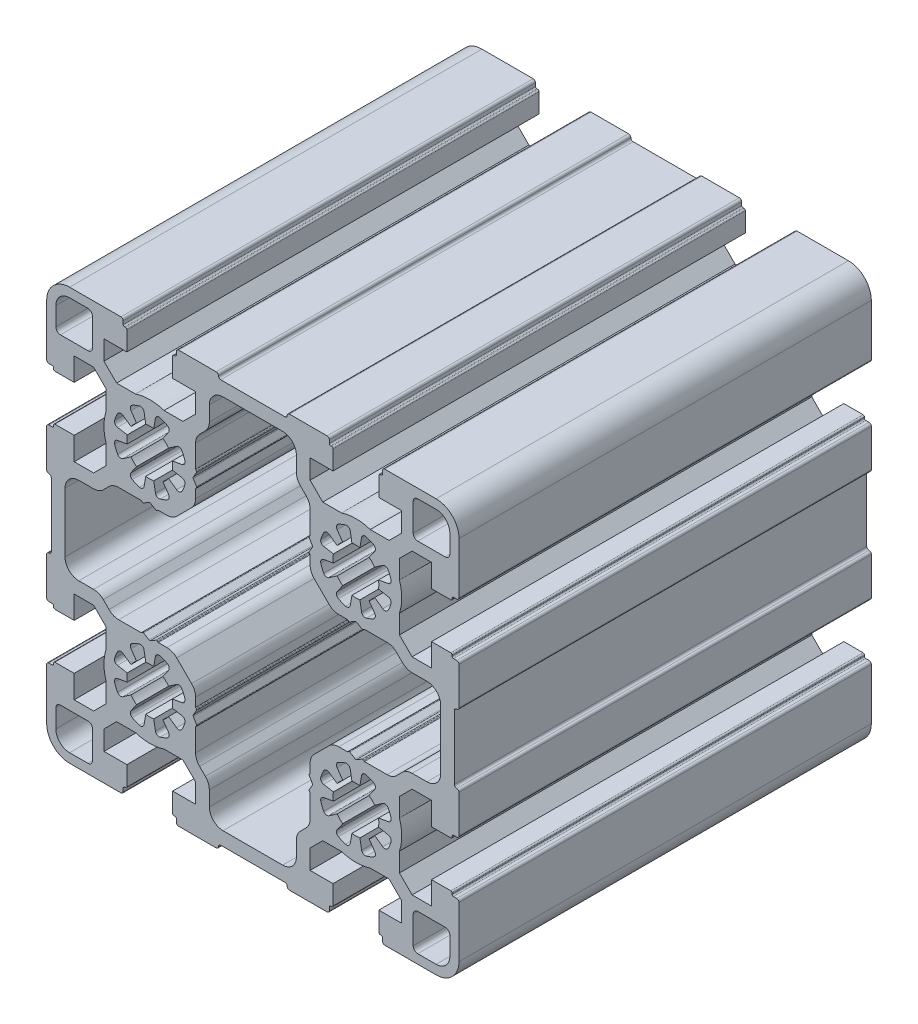
SolidWorks part; units mm, degrees
ref_plane "Front Plane" through (0, 0, 0) normal (0, 0, 1) x (1, 0, 0)
ref_plane "Top Plane" through (0, 0, 0) normal (0, 1, 0) x (1, 0, 0)
ref_plane "Right Plane" through (0, 0, 0) normal (1, 0, 0) x (0, 0, -1)
sketch "Sketch1" plane through (0, 0, 0) normal (0, 0, 1) x (1, 0, 0)
  line L0 (12.5001, -34.7627) -> (15.2628, -32)
  line L1 (15.2628, -32) -> (19.3776, -32)
  line L2 (25.6225, -32) -> (29.7373, -32)
  line L3 (29.7373, -32) -> (32.5, -34.7627)
  line L4 (32.5, -34.7627) -> (32.5, -39)
  line L5 (32.5, -39) -> (27.5002, -39)
  line L6 (27.5002, -39) -> (27.5002, -43.2)
  line L7 (27.8002, -43.5) -> (28.0002, -43.5)
  line L8 (28.3002, -44.5) -> (28.3002, -43.8)
  line L9 (28.8002, -45) -> (40, -45)
  line L10 (45, -40) -> (45, -28.7999)
  line L11 (43.8, -28.2999) -> (44.5, -28.2999)
  line L12 (43.5, -27.9999) -> (43.5, -27.7999)
  line L13 (43.2, -27.4999) -> (39.0002, -27.4999)
  line L14 (39.0002, -27.4999) -> (39.0002, -32.4999)
  line L15 (39.0002, -32.4999) -> (34.7629, -32.4999)
  line L16 (34.7629, -32.4999) -> (32.0002, -29.7372)
  line L17 (32.0002, -29.7372) -> (32.0002, -25.6224)
  line L18 (32.0002, -19.3775) -> (32.0002, -15.2627)
  line L19 (32.0002, -15.2627) -> (34.7629, -12.5)
  line L20 (34.7629, -12.5) -> (39, -12.5)
  line L21 (39, -12.5) -> (39, -17.5)
  line L22 (39, -17.5) -> (43.2, -17.5)
  line L23 (43.5, -17.2) -> (43.5, -17)
  line L24 (43.8, -16.7) -> (44.5, -16.7)
  line L25 (45, -16.2) -> (45, -8)
  line L26 (44, -7) -> (44, 7)
  line L27 (45, 8) -> (45, 16.2)
  line L28 (43.8, 16.7) -> (44.5, 16.7)
  line L29 (43.5, 17) -> (43.5, 17.2)
  line L30 (43.2, 17.5) -> (39.0002, 17.5)
  line L31 (39.0002, 17.5) -> (39.0002, 12.5)
  line L32 (39.0002, 12.5) -> (34.7629, 12.5)
  line L33 (34.7629, 12.5) -> (32.0002, 15.2628)
  line L34 (32.0002, 15.2628) -> (32.0002, 19.3775)
  line L35 (32.0002, 25.6225) -> (32.0002, 29.7372)
  line L36 (32.0002, 29.7372) -> (34.7629, 32.5)
  line L37 (34.7629, 32.5) -> (39, 32.5)
  line L38 (39, 32.5) -> (39, 27.5001)
  line L39 (39, 27.5001) -> (43.2, 27.5001)
  line L40 (43.5, 27.8001) -> (43.5, 28.0001)
  line L41 (43.8, 28.3001) -> (44.5, 28.3001)
  line L42 (45, 28.8001) -> (45, 40)
  line L43 (28.8, 45) -> (40, 45)
  line L44 (28.3, 43.8) -> (28.3, 44.5)
  line L45 (27.8, 43.5) -> (28, 43.5)
  line L46 (27.5, 43.2) -> (27.5, 39)
  line L47 (27.5, 39) -> (32.4999, 39)
  line L48 (32.4999, 39) -> (32.4999, 34.7628)
  line L49 (32.4999, 34.7628) -> (29.7371, 32)
  line L50 (29.7371, 32) -> (25.6224, 32)
  line L51 (19.3774, 32) -> (15.2626, 32)
  line L52 (15.2626, 32) -> (12.4999, 34.7628)
  line L53 (12.4999, 34.7628) -> (12.4999, 39)
  line L54 (12.4999, 39) -> (17.4999, 39)
  line L55 (17.4999, 39) -> (17.4999, 43.2)
  line L56 (16.9999, 43.5) -> (17.1999, 43.5)
  line L57 (16.6999, 43.8) -> (16.6999, 44.5)
  line L58 (7.9999, 45) -> (16.1999, 45)
  line L59 (-7.0001, 44) -> (6.9999, 44)
  line L60 (-16.2, 45) -> (-8.0001, 45)
  line L61 (-16.7, 43.8) -> (-16.7, 44.5)
  line L62 (-17.2, 43.5) -> (-17, 43.5)
  line L63 (-17.5, 43.2) -> (-17.5, 39)
  line L64 (-17.5, 39) -> (-12.5001, 39)
  line L65 (-12.5001, 39) -> (-12.5001, 34.7628)
  line L66 (-12.5001, 34.7628) -> (-15.2628, 32)
  line L67 (-15.2628, 32) -> (-19.3776, 32)
  line L68 (-25.6225, 32) -> (-29.7373, 32)
  line L69 (-29.7373, 32) -> (-32.5, 34.7628)
  line L70 (-32.5, 34.7628) -> (-32.5, 39)
  line L71 (-32.5, 39) -> (-27.5, 39)
  line L72 (-27.5, 39) -> (-27.5, 43.2)
  line L73 (-28, 43.5) -> (-27.8, 43.5)
  line L74 (-28.3, 43.8) -> (-28.3, 44.5)
  line L75 (-40, 45) -> (-28.8, 45)
  line L76 (-45, 28.7999) -> (-45, 40)
  line L77 (-44.5, 28.2999) -> (-43.8, 28.2999)
  line L78 (-43.5, 27.7999) -> (-43.5, 27.9999)
  line L79 (-43.2, 27.4999) -> (-39, 27.4999)
  line L80 (-39, 27.4999) -> (-39, 32.4999)
  line L81 (-39, 32.4999) -> (-34.7628, 32.4999)
  line L82 (-34.7628, 32.4999) -> (-32, 29.7372)
  line L83 (-32, 29.7372) -> (-32, 25.6224)
  line L84 (-32, 19.3775) -> (-32, 15.2627)
  line L85 (-32, 15.2627) -> (-34.7628, 12.5)
  line L86 (-34.7628, 12.5) -> (-39, 12.5)
  line L87 (-39, 12.5) -> (-39, 17.5)
  line L88 (-39, 17.5) -> (-43.2, 17.5)
  line L89 (-43.5, 17) -> (-43.5, 17.2)
  line L90 (-44.5, 16.7) -> (-43.8, 16.7)
  line L91 (-45, 8) -> (-45, 16.2)
  line L92 (-44, -7) -> (-44, 7)
  line L93 (-45, -16.2) -> (-45, -8)
  line L94 (-44.5, -16.7) -> (-43.8, -16.7)
  line L95 (-43.5, -17.2) -> (-43.5, -17)
  line L96 (-43.2, -17.5) -> (-39, -17.5)
  line L97 (-39, -17.5) -> (-39, -12.5)
  line L98 (-39, -12.5) -> (-34.7628, -12.5)
  line L99 (-34.7628, -12.5) -> (-32, -15.2627)
  line L100 (-32, -15.2627) -> (-32, -19.3775)
  line L101 (-32, -25.6224) -> (-32, -29.7372)
  line L102 (-32, -29.7372) -> (-34.7628, -32.4999)
  line L103 (-34.7628, -32.4999) -> (-39, -32.4999)
  line L104 (-39, -32.4999) -> (-39, -27.4999)
  line L105 (-39, -27.4999) -> (-43.2, -27.4999)
  line L106 (-43.5, -27.9999) -> (-43.5, -27.7999)
  line L107 (-44.5, -28.2999) -> (-43.8, -28.2999)
  line L108 (-45, -40) -> (-45, -28.7999)
  line L109 (-40, -45) -> (-28.8, -45)
  line L110 (-28.3, -44.5) -> (-28.3, -43.8)
  line L111 (-28, -43.5) -> (-27.8, -43.5)
  line L112 (-27.5, -43.2) -> (-27.5, -39)
  line L113 (-27.5, -39) -> (-32.5, -39)
  line L114 (-32.5, -39) -> (-32.5, -34.7628)
  line L115 (-32.5, -34.7628) -> (-29.7373, -32)
  line L116 (-29.7373, -32) -> (-25.6225, -32)
  line L117 (-19.3776, -32) -> (-15.2628, -32)
  line L118 (-15.2628, -32) -> (-12.5001, -34.7628)
  line L119 (-12.5001, -34.7628) -> (-12.5001, -39)
  line L120 (-12.5001, -39) -> (-17.5001, -39)
  line L121 (-17.5001, -39) -> (-17.5001, -43.2)
  line L122 (-17.2001, -43.5) -> (-17.0001, -43.5)
  line L123 (-16.7001, -44.5) -> (-16.7001, -43.8)
  line L124 (-16.2001, -45) -> (-8.0001, -45)
  line L125 (-7.0001, -44) -> (6.9999, -44)
  line L126 (7.9999, -45) -> (16.1999, -45)
  line L127 (16.6999, -44.5) -> (16.6999, -43.8)
  line L128 (16.9999, -43.5) -> (17.1999, -43.5)
  line L129 (17.4999, -43.2) -> (17.4999, -39)
  line L130 (17.4999, -39) -> (12.5001, -39)
  line L131 (12.5001, -39) -> (12.5001, -34.7627)
  line L132 (12.2948, -21.1329) -> (12.989, -22.3353)
  line L133 (12.2779, -23.867) -> (12.989, -22.6353)
  line L134 (12.3097, -24.1085) -> (12.4414, -24.2402)
  line L135 (12.5, -29.2774) -> (12.5, -24.3816)
  line L136 (10.3787, -32.6414) -> (11.6213, -31.3987)
  line L137 (9.5, -37.9999) -> (9.5, -34.7627)
  line L138 (-6.5, -40.9999) -> (6.5, -40.9999)
  line L139 (-9.5, -37.9999) -> (-9.5, -34.7627)
  line L140 (-10.3787, -32.6414) -> (-11.6213, -31.3987)
  line L141 (-12.5, -29.2774) -> (-12.5, -24.3816)
  line L142 (-12.4414, -24.2402) -> (-12.3097, -24.1085)
  line L143 (-12.2779, -23.867) -> (-12.989, -22.6353)
  line L144 (-12.989, -22.3353) -> (-12.2948, -21.1329)
  line L145 (-12.3266, -20.8914) -> (-12.4414, -20.7766)
  line L146 (-12.5, -20.6352) -> (-12.5, -18.7426)
  line L147 (-13.3787, -16.6213) -> (-16.6213, -13.3787)
  line L148 (-20.6352, -12.5) -> (-18.7426, -12.5)
  line L149 (-20.7766, -12.4414) -> (-20.8914, -12.3266)
  line L150 (-22.3353, -12.989) -> (-21.1329, -12.2948)
  line L151 (-22.6353, -12.989) -> (-23.867, -12.2779)
  line L152 (-24.2402, -12.4414) -> (-24.1085, -12.3097)
  line L153 (-29.2774, -12.5) -> (-24.3816, -12.5)
  line L154 (-31.3987, -11.6213) -> (-32.6414, -10.3787)
  line L155 (-37.9999, -9.5) -> (-34.7627, -9.5)
  line L156 (-40.9999, -6.5) -> (-40.9999, 6.5)
  line L157 (-37.9999, 9.5) -> (-34.7627, 9.5)
  line L158 (-32.6414, 10.3787) -> (-31.3987, 11.6213)
  line L159 (-29.2774, 12.5) -> (-24.3816, 12.5)
  line L160 (-24.2402, 12.4414) -> (-24.1085, 12.3097)
  line L161 (-23.867, 12.2779) -> (-22.6353, 12.989)
  line L162 (-22.3353, 12.989) -> (-21.1329, 12.2948)
  line L163 (-20.8914, 12.3266) -> (-20.7766, 12.4414)
  line L164 (-20.6352, 12.5) -> (-18.7426, 12.5)
  line L165 (-16.6213, 13.3787) -> (-13.3787, 16.6213)
  line L166 (-12.5, 18.7426) -> (-12.5, 20.6352)
  line L167 (-12.4414, 20.7766) -> (-12.3266, 20.8914)
  line L168 (-12.2948, 21.1329) -> (-12.989, 22.3353)
  line L169 (-12.989, 22.6353) -> (-12.2779, 23.867)
  line L170 (-12.3097, 24.1085) -> (-12.4414, 24.2402)
  line L171 (-12.5, 24.3816) -> (-12.5, 29.2774)
  line L172 (-11.6213, 31.3987) -> (-10.3787, 32.6414)
  line L173 (-9.5, 34.7627) -> (-9.5, 37.9999)
  line L174 (-6.5, 40.9999) -> (6.5, 40.9999)
  line L175 (9.5, 34.7627) -> (9.5, 37.9999)
  line L176 (10.3787, 32.6414) -> (11.6213, 31.3987)
  line L177 (12.5, 24.3816) -> (12.5, 29.2774)
  line L178 (12.3097, 24.1085) -> (12.4414, 24.2402)
  line L179 (12.2779, 23.867) -> (12.989, 22.6353)
  line L180 (12.2948, 21.1329) -> (12.989, 22.3353)
  line L181 (12.3266, 20.8914) -> (12.4414, 20.7766)
  line L182 (12.5, 18.7426) -> (12.5, 20.6352)
  line L183 (13.3787, 16.6213) -> (16.6213, 13.3787)
  line L184 (18.7426, 12.5) -> (20.6352, 12.5)
  line L185 (20.7766, 12.4414) -> (20.8914, 12.3266)
  line L186 (21.1329, 12.2948) -> (22.3353, 12.989)
  line L187 (22.6353, 12.989) -> (23.867, 12.2779)
  line L188 (24.1085, 12.3097) -> (24.2402, 12.4414)
  line L189 (24.3816, 12.5) -> (29.2774, 12.5)
  line L190 (31.3987, 11.6213) -> (32.6414, 10.3787)
  line L191 (34.7627, 9.5) -> (37.9999, 9.5)
  line L192 (40.9999, -6.5) -> (40.9999, 6.5)
  line L193 (34.7627, -9.5) -> (37.9999, -9.5)
  line L194 (31.3987, -11.6213) -> (32.6414, -10.3787)
  line L195 (24.3816, -12.5) -> (29.2774, -12.5)
  line L196 (24.2402, -12.4414) -> (24.1085, -12.3097)
  line L197 (22.6353, -12.989) -> (23.867, -12.2779)
  line L198 (22.3353, -12.989) -> (21.1329, -12.2948)
  line L199 (20.7766, -12.4414) -> (20.8914, -12.3266)
  line L200 (18.7426, -12.5) -> (20.6352, -12.5)
  line L201 (13.3787, -16.6213) -> (16.6213, -13.3787)
  line L202 (12.5, -20.6352) -> (12.5, -18.7426)
  line L203 (12.3266, -20.8914) -> (12.4414, -20.7766)
  line L204 (-18.3958, -28.3613) -> (-19.6321, -26.5957)
  line L205 (-18.4042, -25.3679) -> (-16.6386, -26.6041)
  line L206 (-15.4533, -23.7425) -> (-17.576, -23.3682)
  line L207 (-17.576, -21.6317) -> (-15.4533, -21.2575)
  line L208 (-18.4042, -19.6321) -> (-16.6386, -18.3958)
  line L209 (-19.6321, -18.4043) -> (-18.3958, -16.6387)
  line L210 (-21.6317, -17.576) -> (-21.2574, -15.4533)
  line L211 (-23.3682, -17.576) -> (-23.7425, -15.4533)
  line L212 (-26.6041, -16.6386) -> (-25.3678, -18.4043)
  line L213 (-26.5957, -19.6321) -> (-28.3613, -18.3958)
  line L214 (-29.5466, -21.2575) -> (-27.424, -21.6318)
  line L215 (-29.5466, -23.7425) -> (-27.424, -23.3682)
  line L216 (-28.3613, -26.6042) -> (-26.5957, -25.3679)
  line L217 (-26.6041, -28.3613) -> (-25.3678, -26.5957)
  line L218 (-23.7425, -29.5467) -> (-23.3682, -27.424)
  line L219 (-21.6317, -27.424) -> (-21.2574, -29.5467)
  line L220 (26.6041, -28.3613) -> (25.3678, -26.5957)
  line L221 (26.5957, -25.3678) -> (28.3613, -26.6041)
  line L222 (29.5466, -23.7425) -> (27.4239, -23.3682)
  line L223 (27.4239, -21.6317) -> (29.5466, -21.2575)
  line L224 (26.5957, -19.6321) -> (28.3613, -18.3958)
  line L225 (25.3678, -18.4042) -> (26.6041, -16.6386)
  line L226 (23.3682, -17.576) -> (23.7425, -15.4533)
  line L227 (21.6317, -17.5759) -> (21.2574, -15.4533)
  line L228 (18.3958, -16.6386) -> (19.6321, -18.4042)
  line L229 (18.4042, -19.6321) -> (16.6386, -18.3958)
  line L230 (15.4533, -21.2574) -> (17.5759, -21.6317)
  line L231 (15.4533, -23.7425) -> (17.5759, -23.3682)
  line L232 (16.6386, -26.6041) -> (18.4042, -25.3678)
  line L233 (18.3958, -28.3613) -> (19.6321, -26.5957)
  line L234 (21.2574, -29.5466) -> (21.6317, -27.424)
  line L235 (23.3682, -27.424) -> (23.7425, -29.5466)
  line L236 (-34.9999, -41.9999) -> (-34.9999, -35.9999)
  line L237 (-39.9999, -42.9999) -> (-35.9999, -42.9999)
  line L238 (-42.9999, -39.9999) -> (-42.9999, -35.9999)
  line L239 (-41.9999, -34.9999) -> (-35.9999, -34.9999)
  line L240 (34.9999, -41.9999) -> (34.9999, -35.9999)
  line L241 (35.9999, -42.9999) -> (39.9999, -42.9999)
  line L242 (42.9999, -39.9999) -> (42.9999, -35.9999)
  line L243 (35.9999, -34.9999) -> (41.9999, -34.9999)
  line L244 (-18.3958, 16.6386) -> (-19.6321, 18.4042)
  line L245 (-18.4042, 19.6321) -> (-16.6386, 18.3958)
  line L246 (-15.4532, 21.2574) -> (-17.5759, 21.6317)
  line L247 (-17.5759, 23.3682) -> (-15.4532, 23.7425)
  line L248 (-18.4042, 25.3679) -> (-16.6386, 26.6042)
  line L249 (-19.6321, 26.5957) -> (-18.3958, 28.3613)
  line L250 (-21.6317, 27.424) -> (-21.2574, 29.5467)
  line L251 (-23.3682, 27.424) -> (-23.7425, 29.5467)
  line L252 (-26.6041, 28.3613) -> (-25.3678, 26.5957)
  line L253 (-26.5957, 25.3678) -> (-28.3613, 26.6041)
  line L254 (-29.5467, 23.7425) -> (-27.424, 23.3682)
  line L255 (-29.5467, 21.2574) -> (-27.424, 21.6317)
  line L256 (-28.3613, 18.3958) -> (-26.5957, 19.6321)
  line L257 (-26.6041, 16.6386) -> (-25.3678, 18.4042)
  line L258 (-23.7425, 15.4533) -> (-23.3682, 17.5759)
  line L259 (-21.6317, 17.5759) -> (-21.2574, 15.4533)
  line L260 (26.6041, 16.6386) -> (25.3678, 18.4042)
  line L261 (26.5957, 19.6321) -> (28.3613, 18.3958)
  line L262 (29.5466, 21.2575) -> (27.4239, 21.6317)
  line L263 (27.4239, 23.3682) -> (29.5466, 23.7424)
  line L264 (26.5957, 25.3678) -> (28.3613, 26.6041)
  line L265 (25.3678, 26.5957) -> (26.6041, 28.3613)
  line L266 (23.3682, 27.424) -> (23.7425, 29.5466)
  line L267 (21.6317, 27.424) -> (21.2574, 29.5466)
  line L268 (18.3958, 28.3613) -> (19.6321, 26.5957)
  line L269 (18.4042, 25.3678) -> (16.6386, 26.6041)
  line L270 (15.4533, 23.7425) -> (17.5759, 23.3682)
  line L271 (15.4533, 21.2574) -> (17.5759, 21.6317)
  line L272 (16.6386, 18.3958) -> (18.4042, 19.6321)
  line L273 (18.3958, 16.6386) -> (19.6321, 18.4042)
  line L274 (21.2574, 15.4533) -> (21.6317, 17.5759)
  line L275 (23.3682, 17.576) -> (23.7425, 15.4533)
  line L276 (-34.9999, 35.9999) -> (-34.9999, 41.9999)
  line L277 (-39.9999, 42.9999) -> (-35.9999, 42.9999)
  line L278 (-42.9999, 35.9999) -> (-42.9999, 39.9999)
  line L279 (-41.9999, 34.9999) -> (-35.9999, 34.9999)
  line L280 (34.9999, 35.9999) -> (34.9999, 41.9999)
  line L281 (35.9999, 42.9999) -> (39.9999, 42.9999)
  line L282 (42.9999, 35.9999) -> (42.9999, 39.9999)
  line L283 (35.9999, 34.9999) -> (41.9999, 34.9999)
  line L284 (0, 52.3629) -> (0, -57.313) construction
  line L285 (-58.4117, 0) -> (63.1855, 0) construction
  arc A0 (19.3776, -32) -> (25.6225, -32) centre (22.5, -22.5) ccw
  arc A1 (27.5002, -43.2) -> (27.8002, -43.5) centre (27.8002, -43.2) ccw
  arc A2 (28.3002, -43.8) -> (28.0002, -43.5) centre (28.0002, -43.8) ccw
  arc A3 (28.3002, -44.5) -> (28.8002, -45) centre (28.8002, -44.5) ccw
  arc A4 (40, -45) -> (45, -40) centre (40, -40) ccw
  arc A5 (45, -28.7999) -> (44.5, -28.2999) centre (44.5, -28.7999) ccw
  arc A6 (43.5, -27.9999) -> (43.8, -28.2999) centre (43.8, -27.9999) ccw
  arc A7 (43.5, -27.7999) -> (43.2, -27.4999) centre (43.2, -27.7999) ccw
  arc A8 (32.0002, -25.6224) -> (32.0002, -19.3775) centre (22.5002, -22.5) ccw
  arc A9 (43.2, -17.5) -> (43.5, -17.2) centre (43.2, -17.2) ccw
  arc A10 (43.8, -16.7) -> (43.5, -17) centre (43.8, -17) ccw
  arc A11 (44.5, -16.7) -> (45, -16.2) centre (44.5, -16.2) ccw
  arc A12 (45, -8) -> (44.5, -7.5) centre (44.5, -8) ccw
  arc A13 (44, -7) -> (44.5, -7.5) centre (44.5, -7) ccw
  arc A14 (44.5, 7.5) -> (44, 7) centre (44.5, 7) ccw
  arc A15 (44.5, 7.5) -> (45, 8) centre (44.5, 8) ccw
  arc A16 (45, 16.2) -> (44.5, 16.7) centre (44.5, 16.2) ccw
  arc A17 (43.5, 17) -> (43.8, 16.7) centre (43.8, 17) ccw
  arc A18 (43.5, 17.2) -> (43.2, 17.5) centre (43.2, 17.2) ccw
  arc A19 (32.0002, 19.3775) -> (32.0002, 25.6225) centre (22.5002, 22.5) ccw
  arc A20 (43.2, 27.5001) -> (43.5, 27.8001) centre (43.2, 27.8001) ccw
  arc A21 (43.8, 28.3001) -> (43.5, 28.0001) centre (43.8, 28.0001) ccw
  arc A22 (44.5, 28.3001) -> (45, 28.8001) centre (44.5, 28.8001) ccw
  arc A23 (45, 40) -> (40, 45) centre (40, 40) ccw
  arc A24 (28.8, 45) -> (28.3, 44.5) centre (28.8, 44.5) ccw
  arc A25 (28, 43.5) -> (28.3, 43.8) centre (28, 43.8) ccw
  arc A26 (27.8, 43.5) -> (27.5, 43.2) centre (27.8, 43.2) ccw
  arc A27 (25.6224, 32) -> (19.3774, 32) centre (22.4999, 22.5) ccw
  arc A28 (17.4999, 43.2) -> (17.1999, 43.5) centre (17.1999, 43.2) ccw
  arc A29 (16.6999, 43.8) -> (16.9999, 43.5) centre (16.9999, 43.8) ccw
  arc A30 (16.6999, 44.5) -> (16.1999, 45) centre (16.1999, 44.5) ccw
  arc A31 (7.9999, 45) -> (7.4999, 44.5) centre (7.9999, 44.5) ccw
  arc A32 (6.9999, 44) -> (7.4999, 44.5) centre (6.9999, 44.5) ccw
  arc A33 (-7.5001, 44.5) -> (-7.0001, 44) centre (-7.0001, 44.5) ccw
  arc A34 (-7.5001, 44.5) -> (-8.0001, 45) centre (-8.0001, 44.5) ccw
  arc A35 (-16.2, 45) -> (-16.7, 44.5) centre (-16.2, 44.5) ccw
  arc A36 (-17, 43.5) -> (-16.7, 43.8) centre (-17, 43.8) ccw
  arc A37 (-17.2, 43.5) -> (-17.5, 43.2) centre (-17.2, 43.2) ccw
  arc A38 (-19.3776, 32) -> (-25.6225, 32) centre (-22.5, 22.5) ccw
  arc A39 (-27.5, 43.2) -> (-27.8, 43.5) centre (-27.8, 43.2) ccw
  arc A40 (-28.3, 43.8) -> (-28, 43.5) centre (-28, 43.8) ccw
  arc A41 (-28.3, 44.5) -> (-28.8, 45) centre (-28.8, 44.5) ccw
  arc A42 (-40, 45) -> (-45, 40) centre (-40, 40) ccw
  arc A43 (-45, 28.7999) -> (-44.5, 28.2999) centre (-44.5, 28.7999) ccw
  arc A44 (-43.5, 27.9999) -> (-43.8, 28.2999) centre (-43.8, 27.9999) ccw
  arc A45 (-43.5, 27.7999) -> (-43.2, 27.4999) centre (-43.2, 27.7999) ccw
  arc A46 (-32, 25.6224) -> (-32, 19.3775) centre (-22.5, 22.5) ccw
  arc A47 (-43.2, 17.5) -> (-43.5, 17.2) centre (-43.2, 17.2) ccw
  arc A48 (-43.8, 16.7) -> (-43.5, 17) centre (-43.8, 17) ccw
  arc A49 (-44.5, 16.7) -> (-45, 16.2) centre (-44.5, 16.2) ccw
  arc A50 (-45, 8) -> (-44.5, 7.5) centre (-44.5, 8) ccw
  arc A51 (-44, 7) -> (-44.5, 7.5) centre (-44.5, 7) ccw
  arc A52 (-44.5, -7.5) -> (-44, -7) centre (-44.5, -7) ccw
  arc A53 (-44.5, -7.5) -> (-45, -8) centre (-44.5, -8) ccw
  arc A54 (-45, -16.2) -> (-44.5, -16.7) centre (-44.5, -16.2) ccw
  arc A55 (-43.5, -17) -> (-43.8, -16.7) centre (-43.8, -17) ccw
  arc A56 (-43.5, -17.2) -> (-43.2, -17.5) centre (-43.2, -17.2) ccw
  arc A57 (-32, -19.3775) -> (-32, -25.6224) centre (-22.5, -22.5) ccw
  arc A58 (-43.2, -27.4999) -> (-43.5, -27.7999) centre (-43.2, -27.7999) ccw
  arc A59 (-43.8, -28.2999) -> (-43.5, -27.9999) centre (-43.8, -27.9999) ccw
  arc A60 (-44.5, -28.2999) -> (-45, -28.7999) centre (-44.5, -28.7999) ccw
  arc A61 (-45, -40) -> (-40, -45) centre (-40, -40) ccw
  arc A62 (-28.8, -45) -> (-28.3, -44.5) centre (-28.8, -44.5) ccw
  arc A63 (-28, -43.5) -> (-28.3, -43.8) centre (-28, -43.8) ccw
  arc A64 (-27.8, -43.5) -> (-27.5, -43.2) centre (-27.8, -43.2) ccw
  arc A65 (-25.6225, -32) -> (-19.3776, -32) centre (-22.5, -22.5) ccw
  arc A66 (-17.5001, -43.2) -> (-17.2001, -43.5) centre (-17.2001, -43.2) ccw
  arc A67 (-16.7001, -43.8) -> (-17.0001, -43.5) centre (-17.0001, -43.8) ccw
  arc A68 (-16.7001, -44.5) -> (-16.2001, -45) centre (-16.2001, -44.5) ccw
  arc A69 (-8.0001, -45) -> (-7.5001, -44.5) centre (-8.0001, -44.5) ccw
  arc A70 (-7.0001, -44) -> (-7.5001, -44.5) centre (-7.0001, -44.5) ccw
  arc A71 (7.4999, -44.5) -> (6.9999, -44) centre (6.9999, -44.5) ccw
  arc A72 (7.4999, -44.5) -> (7.9999, -45) centre (7.9999, -44.5) ccw
  arc A73 (16.1999, -45) -> (16.6999, -44.5) centre (16.1999, -44.5) ccw
  arc A74 (16.9999, -43.5) -> (16.6999, -43.8) centre (16.9999, -43.8) ccw
  arc A75 (17.1999, -43.5) -> (17.4999, -43.2) centre (17.1999, -43.2) ccw
  arc A76 (12.3266, -20.8914) -> (12.2948, -21.1329) centre (12.468, -21.0329) ccw
  arc A77 (12.989, -22.6353) -> (12.989, -22.3353) centre (12.7292, -22.4853) ccw
  arc A78 (12.2779, -23.867) -> (12.3097, -24.1085) centre (12.4511, -23.967) ccw
  arc A79 (12.5, -24.3816) -> (12.4414, -24.2402) centre (12.3, -24.3816) ccw
  arc A80 (11.6213, -31.3987) -> (12.5, -29.2774) centre (9.5, -29.2774) ccw
  arc A81 (10.3787, -32.6414) -> (9.5, -34.7627) centre (12.5, -34.7627) ccw
  arc A82 (6.5, -40.9999) -> (9.5, -37.9999) centre (6.5, -37.9999) ccw
  arc A83 (-9.5, -37.9999) -> (-6.5, -40.9999) centre (-6.5, -37.9999) ccw
  arc A84 (-9.5, -34.7627) -> (-10.3787, -32.6414) centre (-12.5, -34.7627) ccw
  arc A85 (-12.5, -29.2774) -> (-11.6213, -31.3987) centre (-9.5, -29.2774) ccw
  arc A86 (-12.4414, -24.2402) -> (-12.5, -24.3816) centre (-12.3, -24.3816) ccw
  arc A87 (-12.3097, -24.1085) -> (-12.2779, -23.867) centre (-12.4511, -23.967) ccw
  arc A88 (-12.989, -22.3353) -> (-12.989, -22.6353) centre (-12.7292, -22.4853) ccw
  arc A89 (-12.2948, -21.1329) -> (-12.3266, -20.8914) centre (-12.468, -21.0329) ccw
  arc A90 (-12.5, -20.6352) -> (-12.4414, -20.7766) centre (-12.3, -20.6352) ccw
  arc A91 (-12.5, -18.7426) -> (-13.3787, -16.6213) centre (-15.5, -18.7426) ccw
  arc A92 (-16.6213, -13.3787) -> (-18.7426, -12.5) centre (-18.7426, -15.5) ccw
  arc A93 (-20.7766, -12.4414) -> (-20.6352, -12.5) centre (-20.6352, -12.3) ccw
  arc A94 (-20.8914, -12.3266) -> (-21.1329, -12.2948) centre (-21.0329, -12.468) ccw
  arc A95 (-22.6353, -12.989) -> (-22.3353, -12.989) centre (-22.4853, -12.7292) ccw
  arc A96 (-23.867, -12.2779) -> (-24.1085, -12.3097) centre (-23.967, -12.4511) ccw
  arc A97 (-24.3816, -12.5) -> (-24.2402, -12.4414) centre (-24.3816, -12.3) ccw
  arc A98 (-31.3987, -11.6213) -> (-29.2774, -12.5) centre (-29.2774, -9.5) ccw
  arc A99 (-32.6414, -10.3787) -> (-34.7627, -9.5) centre (-34.7627, -12.5) ccw
  arc A100 (-40.9999, -6.5) -> (-37.9999, -9.5) centre (-37.9999, -6.5) ccw
  arc A101 (-37.9999, 9.5) -> (-40.9999, 6.5) centre (-37.9999, 6.5) ccw
  arc A102 (-34.7627, 9.5) -> (-32.6414, 10.3787) centre (-34.7627, 12.5) ccw
  arc A103 (-29.2774, 12.5) -> (-31.3987, 11.6213) centre (-29.2774, 9.5) ccw
  arc A104 (-24.2402, 12.4414) -> (-24.3816, 12.5) centre (-24.3816, 12.3) ccw
  arc A105 (-24.1085, 12.3097) -> (-23.867, 12.2779) centre (-23.967, 12.4511) ccw
  arc A106 (-22.3353, 12.989) -> (-22.6353, 12.989) centre (-22.4853, 12.7292) ccw
  arc A107 (-21.1329, 12.2948) -> (-20.8914, 12.3266) centre (-21.0329, 12.468) ccw
  arc A108 (-20.6352, 12.5) -> (-20.7766, 12.4414) centre (-20.6352, 12.3) ccw
  arc A109 (-18.7426, 12.5) -> (-16.6213, 13.3787) centre (-18.7426, 15.5) ccw
  arc A110 (-13.3787, 16.6213) -> (-12.5, 18.7426) centre (-15.5, 18.7426) ccw
  arc A111 (-12.4414, 20.7766) -> (-12.5, 20.6352) centre (-12.3, 20.6352) ccw
  arc A112 (-12.3266, 20.8914) -> (-12.2948, 21.1329) centre (-12.468, 21.0329) ccw
  arc A113 (-12.989, 22.6353) -> (-12.989, 22.3353) centre (-12.7292, 22.4853) ccw
  arc A114 (-12.2779, 23.867) -> (-12.3097, 24.1085) centre (-12.4511, 23.967) ccw
  arc A115 (-12.5, 24.3816) -> (-12.4414, 24.2402) centre (-12.3, 24.3816) ccw
  arc A116 (-11.6213, 31.3987) -> (-12.5, 29.2774) centre (-9.5, 29.2774) ccw
  arc A117 (-10.3787, 32.6414) -> (-9.5, 34.7627) centre (-12.5, 34.7627) ccw
  arc A118 (-6.5, 40.9999) -> (-9.5, 37.9999) centre (-6.5, 37.9999) ccw
  arc A119 (9.5, 37.9999) -> (6.5, 40.9999) centre (6.5, 37.9999) ccw
  arc A120 (9.5, 34.7627) -> (10.3787, 32.6414) centre (12.5, 34.7627) ccw
  arc A121 (12.5, 29.2774) -> (11.6213, 31.3987) centre (9.5, 29.2774) ccw
  arc A122 (12.4414, 24.2402) -> (12.5, 24.3816) centre (12.3, 24.3816) ccw
  arc A123 (12.3097, 24.1085) -> (12.2779, 23.867) centre (12.4511, 23.967) ccw
  arc A124 (12.989, 22.3353) -> (12.989, 22.6353) centre (12.7292, 22.4853) ccw
  arc A125 (12.2948, 21.1329) -> (12.3266, 20.8914) centre (12.468, 21.0329) ccw
  arc A126 (12.5, 20.6352) -> (12.4414, 20.7766) centre (12.3, 20.6352) ccw
  arc A127 (12.5, 18.7426) -> (13.3787, 16.6213) centre (15.5, 18.7426) ccw
  arc A128 (16.6213, 13.3787) -> (18.7426, 12.5) centre (18.7426, 15.5) ccw
  arc A129 (20.7766, 12.4414) -> (20.6352, 12.5) centre (20.6352, 12.3) ccw
  arc A130 (20.8914, 12.3266) -> (21.1329, 12.2948) centre (21.0329, 12.468) ccw
  arc A131 (22.6353, 12.989) -> (22.3353, 12.989) centre (22.4853, 12.7292) ccw
  arc A132 (23.867, 12.2779) -> (24.1085, 12.3097) centre (23.967, 12.4511) ccw
  arc A133 (24.3816, 12.5) -> (24.2402, 12.4414) centre (24.3816, 12.3) ccw
  arc A134 (31.3987, 11.6213) -> (29.2774, 12.5) centre (29.2774, 9.5) ccw
  arc A135 (32.6414, 10.3787) -> (34.7627, 9.5) centre (34.7627, 12.5) ccw
  arc A136 (40.9999, 6.5) -> (37.9999, 9.5) centre (37.9999, 6.5) ccw
  arc A137 (37.9999, -9.5) -> (40.9999, -6.5) centre (37.9999, -6.5) ccw
  arc A138 (34.7627, -9.5) -> (32.6414, -10.3787) centre (34.7627, -12.5) ccw
  arc A139 (29.2774, -12.5) -> (31.3987, -11.6213) centre (29.2774, -9.5) ccw
  arc A140 (24.2402, -12.4414) -> (24.3816, -12.5) centre (24.3816, -12.3) ccw
  arc A141 (24.1085, -12.3097) -> (23.867, -12.2779) centre (23.967, -12.4511) ccw
  arc A142 (22.3353, -12.989) -> (22.6353, -12.989) centre (22.4853, -12.7292) ccw
  arc A143 (21.1329, -12.2948) -> (20.8914, -12.3266) centre (21.0329, -12.468) ccw
  arc A144 (20.6352, -12.5) -> (20.7766, -12.4414) centre (20.6352, -12.3) ccw
  arc A145 (18.7426, -12.5) -> (16.6213, -13.3787) centre (18.7426, -15.5) ccw
  arc A146 (13.3787, -16.6213) -> (12.5, -18.7426) centre (15.5, -18.7426) ccw
  arc A147 (12.4414, -20.7766) -> (12.5, -20.6352) centre (12.3, -20.6352) ccw
  arc A148 (-21.2574, -29.5467) -> (-20.244, -30.1753) centre (-20.4696, -29.4078) ccw
  arc A149 (-20.244, -30.1753) -> (-18.6679, -29.5224) centre (-22.4999, -22.5) ccw
  arc A150 (-18.6679, -29.5224) -> (-18.3958, -28.3613) centre (-19.0511, -28.8202) ccw
  arc A151 (-19.6321, -26.5957) -> (-18.4042, -25.3679) centre (-22.5, -22.5) ccw
  arc A152 (-16.6386, -26.6041) -> (-15.4775, -26.332) centre (-16.1798, -25.9488) ccw
  arc A153 (-15.4775, -26.332) -> (-14.8247, -24.7559) centre (-22.4999, -22.5) ccw
  arc A154 (-14.8247, -24.7559) -> (-15.4533, -23.7425) centre (-15.5922, -24.5303) ccw
  arc A155 (-17.576, -23.3682) -> (-17.576, -21.6317) centre (-22.5, -22.5) ccw
  arc A156 (-15.4533, -21.2575) -> (-14.8247, -20.244) centre (-15.5922, -20.4696) ccw
  arc A157 (-14.8247, -20.244) -> (-15.4775, -18.6679) centre (-22.4999, -22.4999) ccw
  arc A158 (-15.4775, -18.6679) -> (-16.6386, -18.3958) centre (-16.1797, -19.0511) ccw
  arc A159 (-18.4042, -19.6321) -> (-19.6321, -18.4043) centre (-22.5, -22.5) ccw
  arc A160 (-18.3958, -16.6387) -> (-18.6679, -15.4776) centre (-19.0511, -16.1798) ccw
  arc A161 (-18.6679, -15.4776) -> (-20.244, -14.8247) centre (-22.4999, -22.5) ccw
  arc A162 (-20.244, -14.8247) -> (-21.2574, -15.4533) centre (-20.4696, -15.5922) ccw
  arc A163 (-21.6317, -17.576) -> (-23.3682, -17.576) centre (-22.5, -22.5) ccw
  arc A164 (-23.7425, -15.4533) -> (-24.7559, -14.8247) centre (-24.5303, -15.5922) ccw
  arc A165 (-24.7559, -14.8247) -> (-26.332, -15.4775) centre (-22.5, -22.4999) ccw
  arc A166 (-26.332, -15.4775) -> (-26.6041, -16.6386) centre (-25.9488, -16.1798) ccw
  arc A167 (-25.3678, -18.4043) -> (-26.5957, -19.6321) centre (-22.5, -22.5) ccw
  arc A168 (-28.3613, -18.3958) -> (-29.5224, -18.6679) centre (-28.8202, -19.0511) ccw
  arc A169 (-29.5224, -18.6679) -> (-30.1752, -20.244) centre (-22.5, -22.5) ccw
  arc A170 (-30.1752, -20.244) -> (-29.5466, -21.2575) centre (-29.4077, -20.4696) ccw
  arc A171 (-27.424, -21.6318) -> (-27.424, -23.3682) centre (-22.5, -22.5) ccw
  arc A172 (-29.5466, -23.7425) -> (-30.1752, -24.756) centre (-29.4077, -24.5304) ccw
  arc A173 (-30.1752, -24.756) -> (-29.5224, -26.3321) centre (-22.5, -22.5) ccw
  arc A174 (-29.5224, -26.3321) -> (-28.3613, -26.6042) centre (-28.8202, -25.9488) ccw
  arc A175 (-26.5957, -25.3679) -> (-25.3678, -26.5957) centre (-22.5, -22.5) ccw
  arc A176 (-26.6041, -28.3613) -> (-26.332, -29.5224) centre (-25.9488, -28.8202) ccw
  arc A177 (-26.332, -29.5224) -> (-24.7559, -30.1753) centre (-22.5, -22.5) ccw
  arc A178 (-24.7559, -30.1753) -> (-23.7425, -29.5467) centre (-24.5303, -29.4078) ccw
  arc A179 (-23.3682, -27.424) -> (-21.6317, -27.424) centre (-22.5, -22.5) ccw
  arc A180 (23.7425, -29.5466) -> (24.7559, -30.1752) centre (24.5303, -29.4077) ccw
  arc A181 (24.7559, -30.1752) -> (26.332, -29.5224) centre (22.5, -22.5) ccw
  arc A182 (26.332, -29.5224) -> (26.6041, -28.3613) centre (25.9488, -28.8202) ccw
  arc A183 (25.3678, -26.5957) -> (26.5957, -25.3678) centre (22.4999, -22.5) ccw
  arc A184 (28.3613, -26.6041) -> (29.5224, -26.332) centre (28.8201, -25.9488) ccw
  arc A185 (29.5224, -26.332) -> (30.1752, -24.7559) centre (22.5, -22.5) ccw
  arc A186 (30.1752, -24.7559) -> (29.5466, -23.7425) centre (29.4077, -24.5303) ccw
  arc A187 (27.4239, -23.3682) -> (27.4239, -21.6317) centre (22.4999, -22.5) ccw
  arc A188 (29.5466, -21.2575) -> (30.1752, -20.244) centre (29.4077, -20.4696) ccw
  arc A189 (30.1752, -20.244) -> (29.5224, -18.6679) centre (22.5, -22.4999) ccw
  arc A190 (29.5224, -18.6679) -> (28.3613, -18.3958) centre (28.8202, -19.0511) ccw
  arc A191 (26.5957, -19.6321) -> (25.3678, -18.4042) centre (22.4999, -22.5) ccw
  arc A192 (26.6041, -16.6386) -> (26.332, -15.4775) centre (25.9488, -16.1798) ccw
  arc A193 (26.332, -15.4775) -> (24.7559, -14.8247) centre (22.5, -22.4999) ccw
  arc A194 (24.7559, -14.8247) -> (23.7425, -15.4533) centre (24.5303, -15.5922) ccw
  arc A195 (23.3682, -17.576) -> (21.6317, -17.5759) centre (22.4999, -22.5) ccw
  arc A196 (21.2574, -15.4533) -> (20.244, -14.8247) centre (20.4696, -15.5922) ccw
  arc A197 (20.244, -14.8247) -> (18.6679, -15.4775) centre (22.4999, -22.4999) ccw
  arc A198 (18.6679, -15.4775) -> (18.3958, -16.6386) centre (19.0511, -16.1797) ccw
  arc A199 (19.6321, -18.4042) -> (18.4042, -19.6321) centre (22.4999, -22.5) ccw
  arc A200 (16.6386, -18.3958) -> (15.4775, -18.6679) centre (16.1797, -19.0511) ccw
  arc A201 (15.4775, -18.6679) -> (14.8246, -20.244) centre (22.4999, -22.4999) ccw
  arc A202 (14.8246, -20.244) -> (15.4533, -21.2574) centre (15.5922, -20.4696) ccw
  arc A203 (17.5759, -21.6317) -> (17.5759, -23.3682) centre (22.4999, -22.5) ccw
  arc A204 (15.4533, -23.7425) -> (14.8246, -24.7559) centre (15.5922, -24.5303) ccw
  arc A205 (14.8246, -24.7559) -> (15.4775, -26.332) centre (22.4999, -22.5) ccw
  arc A206 (15.4775, -26.332) -> (16.6386, -26.6041) centre (16.1797, -25.9488) ccw
  arc A207 (18.4042, -25.3678) -> (19.6321, -26.5957) centre (22.4999, -22.5) ccw
  arc A208 (18.3958, -28.3613) -> (18.6679, -29.5224) centre (19.0511, -28.8202) ccw
  arc A209 (18.6679, -29.5224) -> (20.244, -30.1752) centre (22.4999, -22.5) ccw
  arc A210 (20.244, -30.1752) -> (21.2574, -29.5466) centre (20.4696, -29.4077) ccw
  arc A211 (21.6317, -27.424) -> (23.3682, -27.424) centre (22.4999, -22.5) ccw
  arc A212 (-34.9999, -35.9999) -> (-35.9999, -34.9999) centre (-35.9999, -35.9999) ccw
  arc A213 (-35.9999, -42.9999) -> (-34.9999, -41.9999) centre (-35.9999, -41.9999) ccw
  arc A214 (-42.9999, -39.9999) -> (-39.9999, -42.9999) centre (-39.9999, -39.9999) ccw
  arc A215 (-41.9999, -34.9999) -> (-42.9999, -35.9999) centre (-41.9999, -35.9999) ccw
  arc A216 (35.9999, -34.9999) -> (34.9999, -35.9999) centre (35.9999, -35.9999) ccw
  arc A217 (34.9999, -41.9999) -> (35.9999, -42.9999) centre (35.9999, -41.9999) ccw
  arc A218 (39.9999, -42.9999) -> (42.9999, -39.9999) centre (39.9999, -39.9999) ccw
  arc A219 (42.9999, -35.9999) -> (41.9999, -34.9999) centre (41.9999, -35.9999) ccw
  arc A220 (-21.2574, 15.4533) -> (-20.244, 14.8246) centre (-20.4696, 15.5922) ccw
  arc A221 (-20.244, 14.8246) -> (-18.6679, 15.4775) centre (-22.4999, 22.4999) ccw
  arc A222 (-18.6679, 15.4775) -> (-18.3958, 16.6386) centre (-19.0511, 16.1797) ccw
  arc A223 (-19.6321, 18.4042) -> (-18.4042, 19.6321) centre (-22.4999, 22.5) ccw
  arc A224 (-16.6386, 18.3958) -> (-15.4775, 18.6679) centre (-16.1797, 19.0511) ccw
  arc A225 (-15.4775, 18.6679) -> (-14.8246, 20.244) centre (-22.4999, 22.4999) ccw
  arc A226 (-14.8246, 20.244) -> (-15.4532, 21.2574) centre (-15.5922, 20.4696) ccw
  arc A227 (-17.5759, 21.6317) -> (-17.5759, 23.3682) centre (-22.4999, 22.5) ccw
  arc A228 (-15.4532, 23.7425) -> (-14.8246, 24.7559) centre (-15.5921, 24.5304) ccw
  arc A229 (-14.8246, 24.7559) -> (-15.4775, 26.332) centre (-22.4998, 22.5) ccw
  arc A230 (-15.4775, 26.332) -> (-16.6386, 26.6042) centre (-16.1797, 25.9488) ccw
  arc A231 (-18.4042, 25.3679) -> (-19.6321, 26.5957) centre (-22.4999, 22.5) ccw
  arc A232 (-18.3958, 28.3613) -> (-18.6679, 29.5224) centre (-19.0511, 28.8202) ccw
  arc A233 (-18.6679, 29.5224) -> (-20.244, 30.1753) centre (-22.4999, 22.5) ccw
  arc A234 (-20.244, 30.1753) -> (-21.2574, 29.5467) centre (-20.4696, 29.4077) ccw
  arc A235 (-21.6317, 27.424) -> (-23.3682, 27.424) centre (-22.4999, 22.5) ccw
  arc A236 (-23.7425, 29.5467) -> (-24.7559, 30.1753) centre (-24.5303, 29.4078) ccw
  arc A237 (-24.7559, 30.1753) -> (-26.332, 29.5224) centre (-22.5, 22.5) ccw
  arc A238 (-26.332, 29.5224) -> (-26.6041, 28.3613) centre (-25.9488, 28.8202) ccw
  arc A239 (-25.3678, 26.5957) -> (-26.5957, 25.3678) centre (-22.4999, 22.5) ccw
  arc A240 (-28.3613, 26.6041) -> (-29.5224, 26.332) centre (-28.8202, 25.9488) ccw
  arc A241 (-29.5224, 26.332) -> (-30.1753, 24.7559) centre (-22.5, 22.5) ccw
  arc A242 (-30.1753, 24.7559) -> (-29.5467, 23.7425) centre (-29.4077, 24.5303) ccw
  arc A243 (-27.424, 23.3682) -> (-27.424, 21.6317) centre (-22.4999, 22.5) ccw
  arc A244 (-29.5467, 21.2574) -> (-30.1753, 20.244) centre (-29.4077, 20.4696) ccw
  arc A245 (-30.1753, 20.244) -> (-29.5224, 18.6679) centre (-22.5, 22.4999) ccw
  arc A246 (-29.5224, 18.6679) -> (-28.3613, 18.3958) centre (-28.8202, 19.0511) ccw
  arc A247 (-26.5957, 19.6321) -> (-25.3678, 18.4042) centre (-22.4999, 22.5) ccw
  arc A248 (-26.6041, 16.6386) -> (-26.332, 15.4775) centre (-25.9488, 16.1797) ccw
  arc A249 (-26.332, 15.4775) -> (-24.7559, 14.8246) centre (-22.5, 22.4999) ccw
  arc A250 (-24.7559, 14.8246) -> (-23.7425, 15.4533) centre (-24.5303, 15.5922) ccw
  arc A251 (-23.3682, 17.5759) -> (-21.6317, 17.5759) centre (-22.4999, 22.5) ccw
  arc A252 (23.7425, 15.4533) -> (24.7559, 14.8247) centre (24.5303, 15.5922) ccw
  arc A253 (24.7559, 14.8247) -> (26.332, 15.4775) centre (22.5, 22.4999) ccw
  arc A254 (26.332, 15.4775) -> (26.6041, 16.6386) centre (25.9488, 16.1798) ccw
  arc A255 (25.3678, 18.4042) -> (26.5957, 19.6321) centre (22.4999, 22.5) ccw
  arc A256 (28.3613, 18.3958) -> (29.5224, 18.6679) centre (28.8201, 19.0511) ccw
  arc A257 (29.5224, 18.6679) -> (30.1752, 20.244) centre (22.5, 22.4999) ccw
  arc A258 (30.1752, 20.244) -> (29.5466, 21.2575) centre (29.4077, 20.4696) ccw
  arc A259 (27.4239, 21.6317) -> (27.4239, 23.3682) centre (22.4999, 22.5) ccw
  arc A260 (29.5466, 23.7424) -> (30.1752, 24.7559) centre (29.4077, 24.5303) ccw
  arc A261 (30.1752, 24.7559) -> (29.5224, 26.332) centre (22.5, 22.5) ccw
  arc A262 (29.5224, 26.332) -> (28.3613, 26.6041) centre (28.8201, 25.9488) ccw
  arc A263 (26.5957, 25.3678) -> (25.3678, 26.5957) centre (22.4999, 22.5) ccw
  arc A264 (26.6041, 28.3613) -> (26.332, 29.5224) centre (25.9488, 28.8202) ccw
  arc A265 (26.332, 29.5224) -> (24.7559, 30.1753) centre (22.5, 22.5) ccw
  arc A266 (24.7559, 30.1753) -> (23.7425, 29.5466) centre (24.5303, 29.4077) ccw
  arc A267 (23.3682, 27.424) -> (21.6317, 27.424) centre (22.4999, 22.5) ccw
  arc A268 (21.2574, 29.5466) -> (20.244, 30.1753) centre (20.4696, 29.4077) ccw
  arc A269 (20.244, 30.1753) -> (18.6679, 29.5224) centre (22.4999, 22.5) ccw
  arc A270 (18.6679, 29.5224) -> (18.3958, 28.3613) centre (19.0511, 28.8202) ccw
  arc A271 (19.6321, 26.5957) -> (18.4042, 25.3678) centre (22.4999, 22.5) ccw
  arc A272 (16.6386, 26.6041) -> (15.4775, 26.332) centre (16.1797, 25.9488) ccw
  arc A273 (15.4775, 26.332) -> (14.8246, 24.7559) centre (22.4999, 22.5) ccw
  arc A274 (14.8246, 24.7559) -> (15.4533, 23.7425) centre (15.5922, 24.5303) ccw
  arc A275 (17.5759, 23.3682) -> (17.5759, 21.6317) centre (22.4999, 22.5) ccw
  arc A276 (15.4533, 21.2574) -> (14.8246, 20.244) centre (15.5922, 20.4696) ccw
  arc A277 (14.8246, 20.244) -> (15.4775, 18.6679) centre (22.4999, 22.4999) ccw
  arc A278 (15.4775, 18.6679) -> (16.6386, 18.3958) centre (16.1797, 19.0511) ccw
  arc A279 (18.4042, 19.6321) -> (19.6321, 18.4042) centre (22.4999, 22.5) ccw
  arc A280 (18.3958, 16.6386) -> (18.6679, 15.4775) centre (19.0511, 16.1797) ccw
  arc A281 (18.6679, 15.4775) -> (20.244, 14.8247) centre (22.4999, 22.4999) ccw
  arc A282 (20.244, 14.8247) -> (21.2574, 15.4533) centre (20.4696, 15.5922) ccw
  arc A283 (21.6317, 17.5759) -> (23.3682, 17.576) centre (22.4999, 22.5) ccw
  arc A284 (-35.9999, 34.9999) -> (-34.9999, 35.9999) centre (-35.9999, 35.9999) ccw
  arc A285 (-34.9999, 41.9999) -> (-35.9999, 42.9999) centre (-35.9999, 41.9999) ccw
  arc A286 (-39.9999, 42.9999) -> (-42.9999, 39.9999) centre (-39.9999, 39.9999) ccw
  arc A287 (-42.9999, 35.9999) -> (-41.9999, 34.9999) centre (-41.9999, 35.9999) ccw
  arc A288 (34.9999, 35.9999) -> (35.9999, 34.9999) centre (35.9999, 35.9999) ccw
  arc A289 (35.9999, 42.9999) -> (34.9999, 41.9999) centre (35.9999, 41.9999) ccw
  arc A290 (42.9999, 39.9999) -> (39.9999, 42.9999) centre (39.9999, 39.9999) ccw
  arc A291 (41.9999, 34.9999) -> (42.9999, 35.9999) centre (41.9999, 35.9999) ccw
  point P672 (-44.9999, -44.9999)
  point P673 (-22.5, -44.9999)
  point P686 (0, -44.9999)
  point P687 (22.5, -44.9999)
  point P688 (44.9999, -44.9999)
  point P689 (-44.9999, -22.5)
  point P690 (-22.5, -22.5)
  point P691 (-44.9999, 0)
  point P692 (22.5, -22.5)
  point P693 (44.9999, -22.5)
  point P694 (0, 0)
  point P695 (44.9999, 0)
  point P856 (-44.9999, 22.5)
  point P857 (-22.5, 22.5)
  point P858 (22.5, 22.5)
  point P859 (44.9999, 22.5)
  point P872 (-44.9999, 44.9999)
  point P873 (-22.5, 44.9999)
  point P886 (0, 44.9999)
  point P887 (22.5, 44.9999)
  point P888 (44.9999, 44.9999)
  dimension "D3" = 10
  dimension "D1" = 90
  dimension "D2" = 90
  dimension "D4" = 22.5
  dimension "D5" = 45
  dimension "D6" = 10
  dimension "D7" = 45
extrude "Base-Extrude" add sketch "Sketch1" against normal blind 90
sketch "Эскиз1" plane through (0, 45, 0) normal (0, 1, 0) x (1, 0, 0)
  circle A0 centre (-22.5, 22.5) radius 8.6
  dimension "D1" = 22.5
